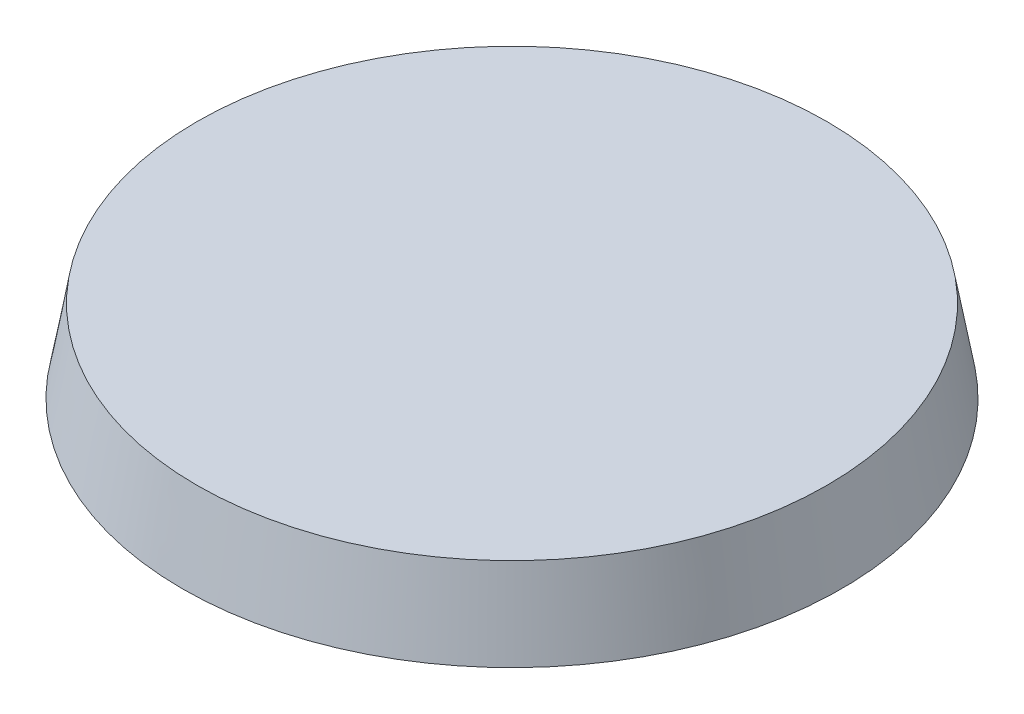
SolidWorks part; units mm, degrees
ref_plane "Спереди" through (0, 0, 0) normal (0, 0, 1) x (1, 0, 0)
ref_plane "Сверху" through (0, 0, 0) normal (0, 1, 0) x (1, 0, 0)
ref_plane "Справа" through (0, 0, 0) normal (1, 0, 0) x (0, 0, -1)
sketch "Эскиз1" plane through (0, 0, 0) normal (0, 1, 0) x (1, 0, 0)
  circle A0 centre (0, 0) radius 14
extrude "Бобышка-Вытянуть1" add sketch "Эскиз1" along normal blind 3.5 draft 10
